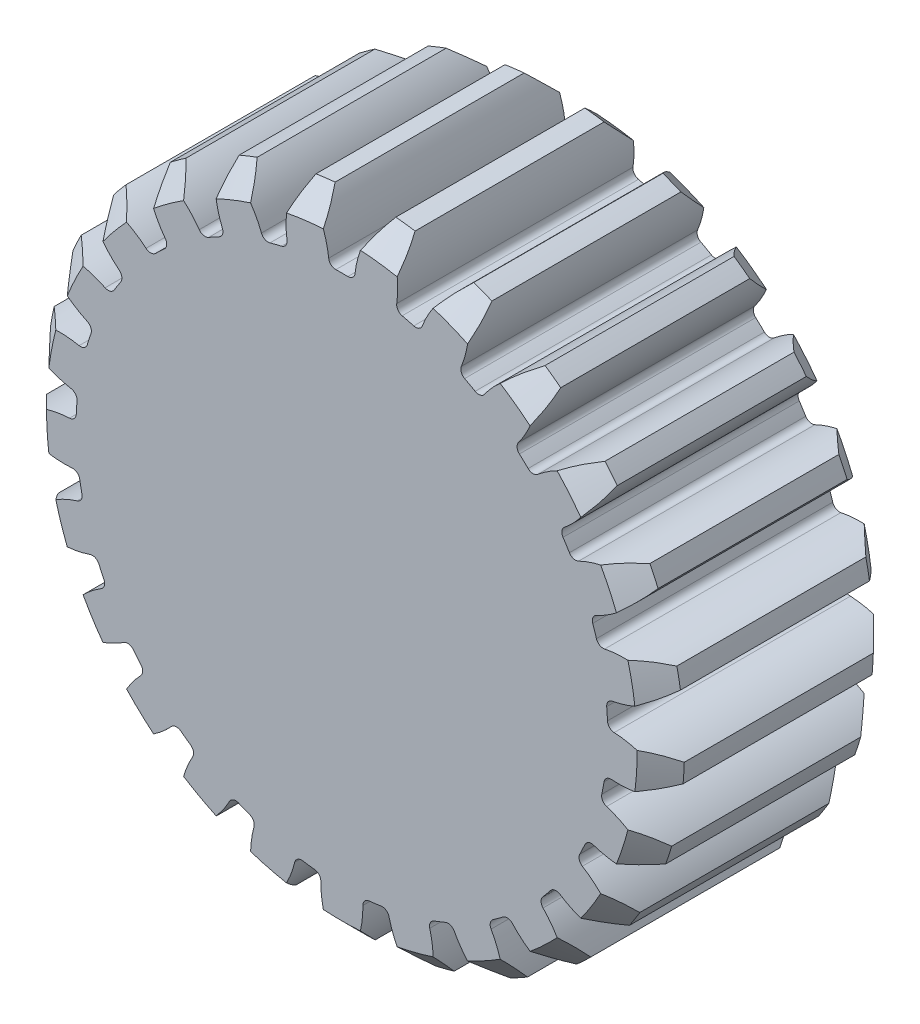
SolidWorks part; units mm, degrees
ref_plane "Plan de face" through (0, 0, 0) normal (0, 0, 1) x (1, 0, 0)
ref_plane "Plan de dessus" through (0, 0, 0) normal (0, 1, 0) x (1, 0, 0)
ref_plane "Plan de droite" through (0, 0, 0) normal (1, 0, 0) x (0, 0, -1)
sketch "Sketch1" plane through (0, 0, 0) normal (0, 0, 1) x (1, 0, 0)
  circle A1 centre (0, 0) radius 27
  dimension "addendumD" = 54
extrude "Boss-Extrude1" add sketch "Sketch1" along normal mid plane 20
sketch "Sketch3" plane through (0, 0, 10) normal (0, 0, 1) x (1, 0, 0)
  line L0 (0, 0) -> (0, 27) construction
  line L1 (0, 0) -> (6.7146, 26.1517) construction
  line L2 (0, 0) -> (3.384, 26.7871) construction
  line L3 (0, 0) -> (-1.072, 22.4744) construction
  line L4 (-1.5698, 24.9507) -> (1.5698, 24.9507) construction
  line L5 (1.5698, 24.9507) -> (4.6845, 24.5572) construction
  line L6 (-2.2805, 26.9035) -> (0, 20.6378) construction
  circle A0 centre (0, 0) radius 25 construction
  circle A1 centre (0, 0) radius 23 construction
  circle A2 centre (0, 0) radius 27 construction
  arc A4 (-2.5691, 26.8775) -> (-1.072, 22.4744) centre (-9.4743, 22.0737) cw
  arc A5 (2.5691, 26.8775) -> (1.072, 22.4744) centre (9.4743, 22.0737) ccw
  arc A6 (1.072, 22.4744) -> (-1.072, 22.4744) centre (0, 0) ccw
  arc A7 (2.5691, 26.8775) -> (-2.5691, 26.8775) centre (0, 0) ccw
  dimension "PitchD" = 50
  dimension "Addendum&dedendum" = 4
  dimension "ToothAngle" = 14.4
  dimension "PressureAngle" = 20
  dimension "Dedendum" = 2.5
extrude "Cut-Extrude2" cut sketch "Sketch3" against normal up to next (20 mm away)
fillet "Fillet2" radius 0.6 2 edges at (1.072, 22.4744, 0) (-1.072, 22.4744, 0)
chamfer "Chamfer1" distance 2 angle 45 2 edges at (0, -27, -10) (0, -27, 10)
pattern_circular "CirPattern1" count 25 over 360 about axis through (0, 0, 0) along (0, 0, 1) of "Fillet2", "Cut-Extrude2"
equation "\"Module\"= 2mm"
equation "\"Number of teeth\"= 25"
equation "\"Pressre angle\"= 20mm"
equation "\"addendumD@Sketch1\"=( \"Module\" * \"Number of teeth\" )  + 2 * \"Module\""
equation "\"PitchD@Sketch3\"=\"Module\" * \"Number of teeth\""
equation "\"ToothAngle@Sketch3\"=360 / \"Number of teeth\""
equation "\"PressureAngle@Sketch3\"=\"Pressre angle\""
equation "\"FilletR@Fillet2\"=0.3 * \"Module\""
equation "\"TeethNo@CirPattern1\"=\"Number of teeth\""
equation "\"ChamferDis@Chamfer1\"=\"Module\""
equation "\"Addendum&dedendum@Sketch3\"=2 * \"Module\""
equation "\"Dedendum@Sketch3\"=( 1.25 * \"Module\" )"
